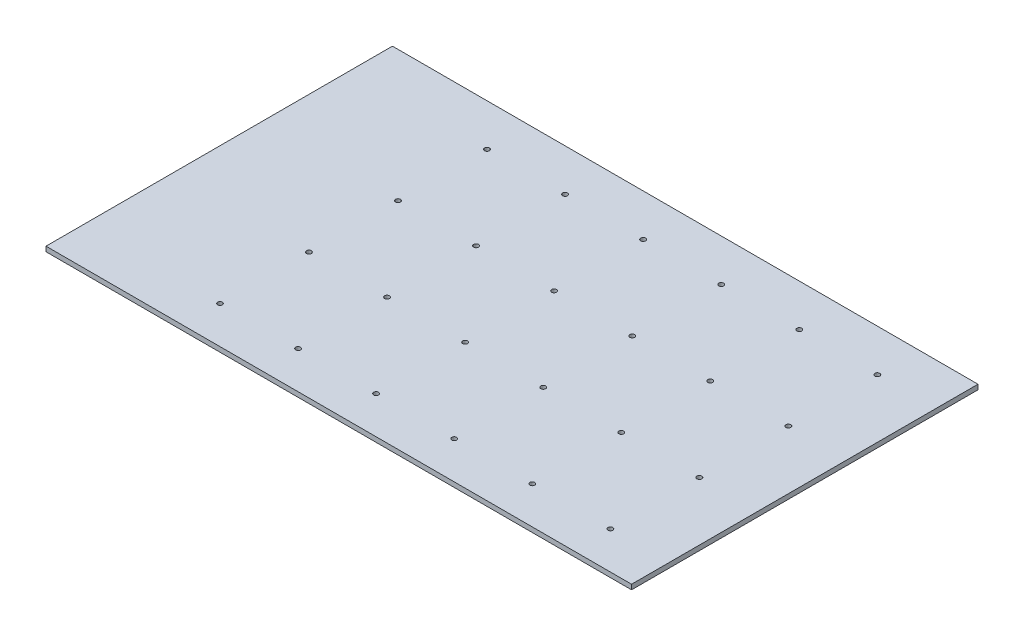
SolidWorks part; units mm, degrees
material "Acrylic (Medium-high impact)"
ref_plane "Front Plane" through (0, 0, 0) normal (0, 0, 1) x (1, 0, 0)
ref_plane "Top Plane" through (0, 0, 0) normal (0, 1, 0) x (1, 0, 0)
ref_plane "Right Plane" through (0, 0, 0) normal (1, 0, 0) x (0, 0, -1)
sketch "Sketch1" plane through (0, 0, 0) normal (0, 1, 0) x (1, 0, 0)
  line L1 (0, 0) -> (762, 0)
  line L2 (0, 0) -> (0, 450.85)
  line L3 (0, 450.85) -> (762, 450.85)
  line L4 (762, 0) -> (762, 450.85)
  dimension "D1" = 450.85
  dimension "D2" = 762
extrude "Boss-Extrude1" add sketch "Sketch1" along normal blind 6.35
sketch "Sketch2" plane through (0, 6.35, 0) normal (0, 1, 0) x (1, 0, 0)
  line L0 (0, 396.0876) -> (762, 396.0876) construction
  line L1 (0, 450.85) -> (0, 0) construction
  line L2 (762, 0) -> (762, 450.85) construction
  line L3 (762, 450.85) -> (0, 450.85) construction
  line L4 (0, 280.1874) -> (762, 280.1874) construction
  line L5 (0, 164.2872) -> (762, 164.2872) construction
  line L6 (0, 48.387) -> (762, 48.387) construction
  circle A0 centre (177.8, 396.0876) radius 3.175
  circle A1 centre (279.4, 396.0876) radius 3.175
  circle A2 centre (381, 396.0876) radius 3.175
  circle A3 centre (482.6, 396.0876) radius 3.175
  circle A4 centre (177.8, 280.2636) radius 3.175
  circle A5 centre (279.4, 280.2636) radius 3.175
  circle A6 centre (381, 280.2636) radius 3.175
  circle A7 centre (482.6, 280.2636) radius 3.175
  circle A8 centre (177.8, 164.4396) radius 3.175
  circle A9 centre (279.4, 164.4396) radius 3.175
  circle A10 centre (381, 164.4396) radius 3.175
  circle A11 centre (482.6, 164.4396) radius 3.175
  circle A12 centre (177.8, 48.6156) radius 3.175
  circle A13 centre (279.4, 48.6156) radius 3.175
  circle A14 centre (381, 48.6156) radius 3.175
  circle A15 centre (482.6, 48.6156) radius 3.175
  circle A16 centre (584.2, 396.0876) radius 3.175
  circle A17 centre (685.8, 396.0876) radius 3.175
  circle A18 centre (584.2, 280.2636) radius 3.175
  circle A19 centre (685.8, 280.2636) radius 3.175
  circle A20 centre (584.2, 164.4396) radius 3.175
  circle A21 centre (685.8, 164.4396) radius 3.175
  circle A22 centre (584.2, 48.6156) radius 3.175
  circle A23 centre (685.8, 48.6156) radius 3.175
  dimension "D4" = 6.35
  dimension "D1" = 54.7624
  dimension "D3" = 115.9002
  dimension "D5" = 177.8
  dimension "D7" = 101.6
  dimension "D9" = 115.824
  dimension "D2" = 4
  dimension "D6" = 6
  dimension "D8" = 4
  dimension "D10" = 4
extrude "Cut-Extrude1" cut sketch "Sketch2" against normal blind 6.35
